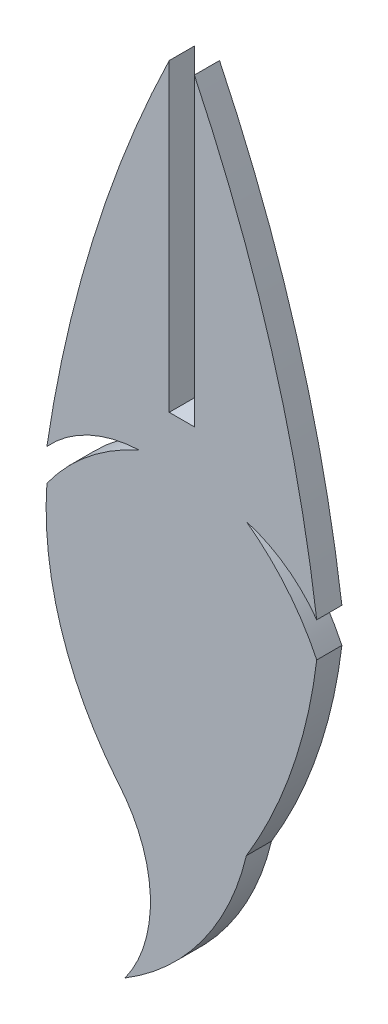
SolidWorks part; units mm, degrees
ref_plane "Front Plane" through (0, 0, 0) normal (0, 0, 1) x (1, 0, 0)
ref_plane "Top Plane" through (0, 0, 0) normal (0, 1, 0) x (1, 0, 0)
ref_plane "Right Plane" through (0, 0, 0) normal (1, 0, 0) x (0, 0, -1)
sketch "Sketch1" plane through (0, 0, 0) normal (0, 0, 1) x (1, 0, 0)
  line L0 (-1.524, -34.6762) -> (0, -34.6762)
  line L1 (0, -34.6762) -> (0, -16.2071)
  line L2 (-0.762, -34.6762) -> (-0.762, -15.1233) construction
  line L3 (-1.524, -16.2071) -> (-1.524, -34.6762)
  arc A0 (0, -16.2071) -> (7.416, -41.0978) centre (-74.6855, -52.0094) cw
  arc A1 (7.416, -41.0978) -> (3.1505, -38.0684) centre (0.9076, -45.7444) ccw
  arc A2 (3.1505, -38.0684) -> (7.416, -43.2036) centre (-4.8908, -49.0871) cw
  arc A3 (7.416, -43.2036) -> (3.1505, -55.6111) centre (-23.666, -39.4551) cw
  arc A4 (-8.94, -42.1077) -> (-4.6745, -55.6111) centre (10.271, -43.4647) ccw
  arc A5 (-3.3374, -37.5674) -> (-8.94, -42.1077) centre (2.1441, -50.0584) ccw
  arc A6 (-8.94, -40.1751) -> (-3.3374, -37.5674) centre (-3.0263, -45.5583) cw
  arc A7 (-1.524, -16.2071) -> (-8.94, -40.1751) centre (72.9777, -52.3903) ccw
  arc A8 (-4.6745, -55.6111) -> (-4.2086, -65.7125) centre (-10.7725, -60.9538) cw
  arc A9 (-4.2086, -65.7125) -> (3.1505, -55.6111) centre (-12.6066, -51.863) ccw
extrude "Boss-Extrude1" add sketch "Sketch1" along normal blind 1.524
